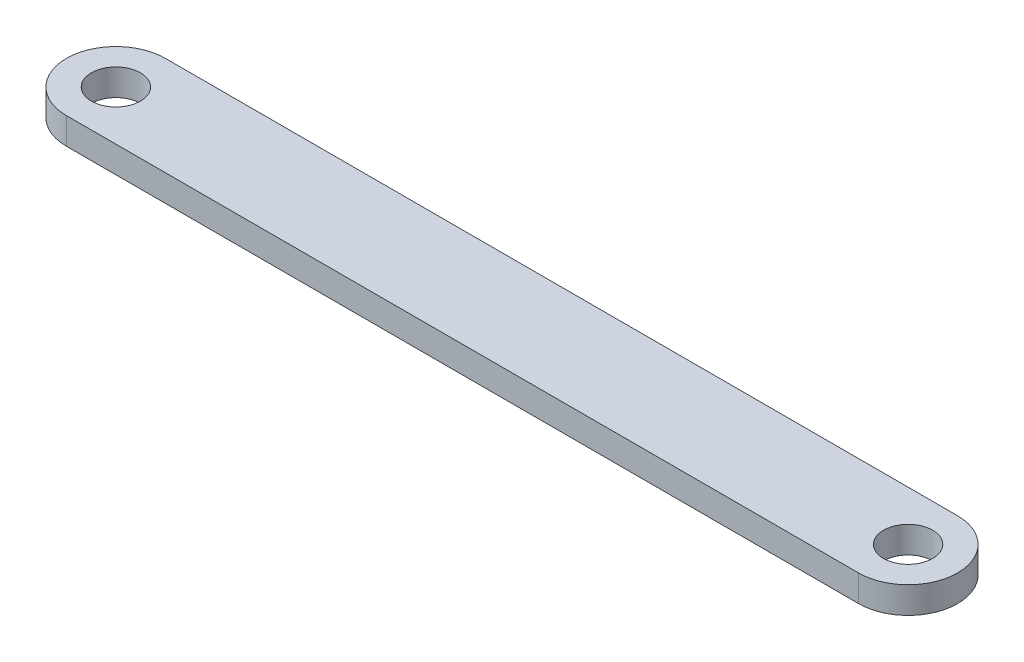
SolidWorks part; units mm, degrees
ref_plane "Front Plane" through (0, 0, 0) normal (0, 0, 1) x (1, 0, 0)
ref_plane "Top Plane" through (0, 0, 0) normal (0, 1, 0) x (1, 0, 0)
ref_plane "Right Plane" through (0, 0, 0) normal (1, 0, 0) x (0, 0, -1)
sketch "Sketch1" plane through (0, 0, 0) normal (0, 1, 0) x (1, 0, 0)
  line L0 (0, 0) -> (193.7053, 0) construction
  line L1 (0, 12.1066) -> (193.7053, 12.1066)
  line L2 (0, -12.1066) -> (193.7053, -12.1066)
  arc A0 (0, 12.1066) -> (0, -12.1066) centre (0, 0) ccw
  arc A1 (193.7053, -12.1066) -> (193.7053, 12.1066) centre (193.7053, 0) ccw
  circle A2 centre (0, 0) radius 6
  circle A3 centre (193.7053, 0) radius 6
  point P3 (96.8526, 0)
  dimension "D1" = 12
  dimension "D2" = 12
extrude "Boss-Extrude1" add sketch "Sketch1" along normal blind 6.5 contours A3 | A2 | L1 A1 L2 A0
